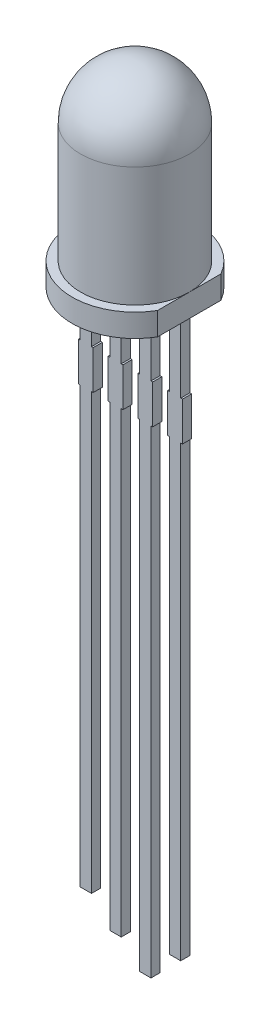
SolidWorks part; units mm, degrees
ref_plane "Front" through (0, 0, 0) normal (0, 0, 1) x (1, 0, 0)
ref_plane "Top" through (0, 0, 0) normal (0, 1, 0) x (1, 0, 0)
ref_plane "Right" through (0, 0, 0) normal (1, 0, 0) x (0, 0, -1)
sketch "Sketch1" plane through (0, 0, 0) normal (0, 0, 1) x (1, 0, 0)
  line L0 (0, 0) -> (0, -2989.7799) construction
  line L1 (0, 0) -> (2.75, 0)
  line L2 (2.75, 0) -> (2.75, 1)
  line L3 (2.75, 1) -> (2.375, 1)
  line L4 (2.375, 1) -> (2.375, 6.225)
  line L5 (0, 8.6) -> (0, 0)
  arc A0 (2.375, 6.225) -> (0, 8.6) centre (0, 6.225) ccw
  dimension "D1" = 4.75
  dimension "D2" = 1
  dimension "D3" = 5.5
  dimension "D4" = 8.6
revolve "Revolve1" add sketch "Sketch1" angle 360 about L0
sketch "Sketch2" plane through (0, 0, 0) normal (0, 0, 1) x (1, 0, 0)
  line L0 (-2.75, 0) -> (2.75, 0) construction
  line L1 (2.2, -24.3) -> (1.7, -24.3)
  line L2 (2.2, -24.3) -> (2.2, 0)
  line L3 (2.2, 0) -> (1.7, 0)
  line L4 (1.7, -24.3) -> (1.7, 0)
  line L5 (2.2, -24.3) -> (1.7, 0) construction
  line L6 (2.2, 0) -> (1.7, -24.3) construction
  line L7 (0, 0) -> (0, -50000) construction
  line L8 (0.9, -25.6) -> (0.4, -25.6)
  line L9 (0.9, -25.6) -> (0.9, 0)
  line L10 (0.9, 0) -> (0.4, 0)
  line L11 (0.4, -25.6) -> (0.4, 0)
  line L12 (0.9, -25.6) -> (0.4, 0) construction
  line L13 (0.9, 0) -> (0.4, -25.6) construction
  line L14 (-0.4, -24.7) -> (-0.9, -24.7)
  line L15 (-0.4, -24.7) -> (-0.4, 0)
  line L16 (-0.4, 0) -> (-0.9, 0)
  line L17 (-0.9, -24.7) -> (-0.9, 0)
  line L18 (-0.4, -24.7) -> (-0.9, 0) construction
  line L19 (-0.4, 0) -> (-0.9, -24.7) construction
  line L20 (-1.7, -23.7) -> (-2.2, -23.7)
  line L21 (-1.7, -23.7) -> (-1.7, 0)
  line L22 (-1.7, 0) -> (-2.2, 0)
  line L23 (-2.2, -23.7) -> (-2.2, 0)
  line L24 (-1.7, -23.7) -> (-2.2, 0) construction
  line L25 (-1.7, 0) -> (-2.2, -23.7) construction
  line L26 (1.95, 0) -> (0.65, 0) construction
  line L27 (0.65, 0) -> (-0.65, 0) construction
  line L29 (-1.625, -3) -> (-2.275, -3)
  line L30 (-1.625, -3) -> (-1.625, -4.7)
  line L31 (-1.625, -4.7) -> (-2.275, -4.7)
  line L32 (-2.275, -3) -> (-2.275, -4.7)
  line L33 (-1.625, -3) -> (-2.275, -4.7) construction
  line L34 (-1.625, -4.7) -> (-2.275, -3) construction
  line L35 (-0.325, -3) -> (-0.975, -3)
  line L36 (-0.325, -3) -> (-0.325, -4.7)
  line L37 (-0.325, -4.7) -> (-0.975, -4.7)
  line L38 (-0.975, -3) -> (-0.975, -4.7)
  line L39 (-0.325, -3) -> (-0.975, -4.7) construction
  line L40 (-0.325, -4.7) -> (-0.975, -3) construction
  line L41 (0.975, -3) -> (0.325, -3)
  line L42 (0.975, -3) -> (0.975, -4.7)
  line L43 (0.975, -4.7) -> (0.325, -4.7)
  line L44 (0.325, -3) -> (0.325, -4.7)
  line L45 (0.975, -3) -> (0.325, -4.7) construction
  line L46 (0.975, -4.7) -> (0.325, -3) construction
  line L47 (2.275, -3) -> (1.625, -3)
  line L48 (2.275, -3) -> (2.275, -4.7)
  line L49 (2.275, -4.7) -> (1.625, -4.7)
  line L50 (1.625, -3) -> (1.625, -4.7)
  line L51 (2.275, -3) -> (1.625, -4.7) construction
  line L52 (2.275, -4.7) -> (1.625, -3) construction
  point P0 (1.95, -12.15)
  point P7 (0.65, -12.8)
  point P12 (-0.65, -12.35)
  point P17 (-1.95, -11.85)
  point P27 (-1.95, -3.85)
  point P28 (0.65, 0)
  point P29 (1.95, 0)
  point P35 (-0.65, -3.85)
  point P40 (0.65, -3.85)
  point P45 (1.95, -3.85)
  point P51 (-1.95, 0)
  dimension "D1" = 0.5
  dimension "D2" = 1.3
  dimension "D3" = 24.3
  dimension "D4" = 25.6
  dimension "D5" = 24.7
  dimension "D6" = 23.7
  dimension "D7" = 0.65
  dimension "D8" = 1.7
  dimension "D9" = 3
extrude "Boss-Extrude1" add sketch "Sketch2" along normal mid plane 0.4 contours L32 L31 L30 L29 | L23 L22 L21 L20 | L37 L38 L35 L36 | L17 L16 L15 L14 | L43 L44 L41 L42 | L11 L10 L9 L8 | L49 L50 L47 L48 | L4 L3 L2 L1
sketch "Sketch3" plane through (0, 1, 0) normal (0, 1, 0) x (1, 0, 0)
  line L0 (2.375, 1.3863) -> (2.375, -1.3863)
  circle A0 centre (0, 0) radius 2.75 construction
  circle A1 centre (0, 0) radius 2.375 construction
extrude "Cut-Extrude1" cut sketch "Sketch3" against normal through all
